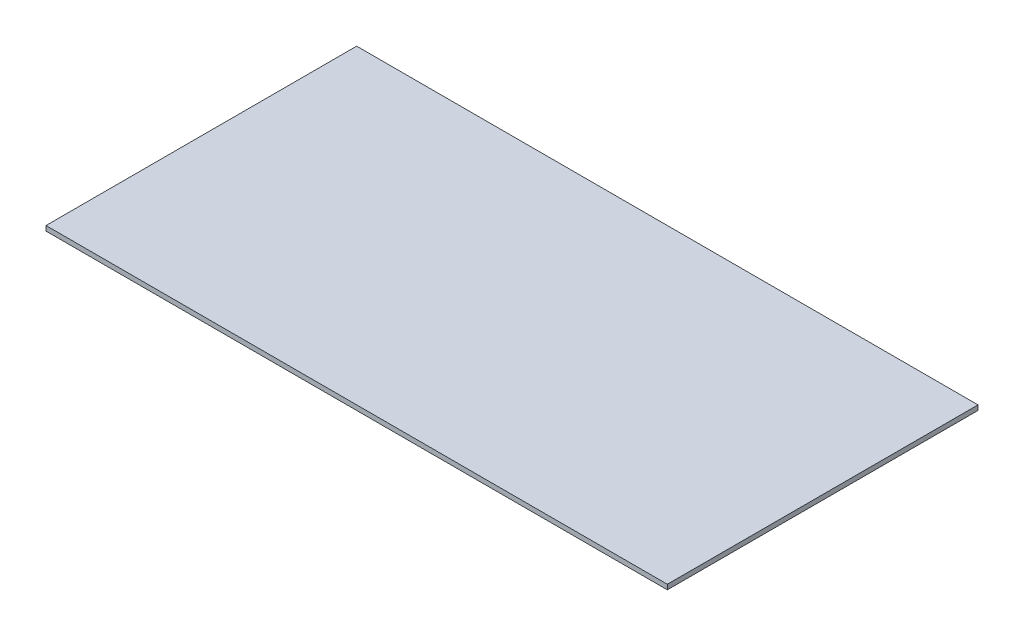
SolidWorks part; units mm, degrees
ref_plane "Front Plane" through (0, 0, 0) normal (0, 0, 1) x (1, 0, 0)
ref_plane "Top Plane" through (0, 0, 0) normal (0, 1, 0) x (1, 0, 0)
ref_plane "Right Plane" through (0, 0, 0) normal (1, 0, 0) x (0, 0, -1)
sketch "Sketch1" plane through (0, 0, 0) normal (0, 1, 0) x (1, 0, 0)
  line L1 (1219.2, 609.6) -> (-1219.2, 609.6)
  line L2 (1219.2, 609.6) -> (1219.2, -609.6)
  line L3 (1219.2, -609.6) -> (-1219.2, -609.6)
  line L4 (-1219.2, 609.6) -> (-1219.2, -609.6)
  line L5 (1219.2, 609.6) -> (-1219.2, -609.6) construction
  line L6 (1219.2, -609.6) -> (-1219.2, 609.6) construction
  point P0 (0, 0)
  dimension "D1" = 1219.2
  dimension "D2" = 2438.4
extrude "Boss-Extrude1" add sketch "Sketch1" along normal blind 19.05
